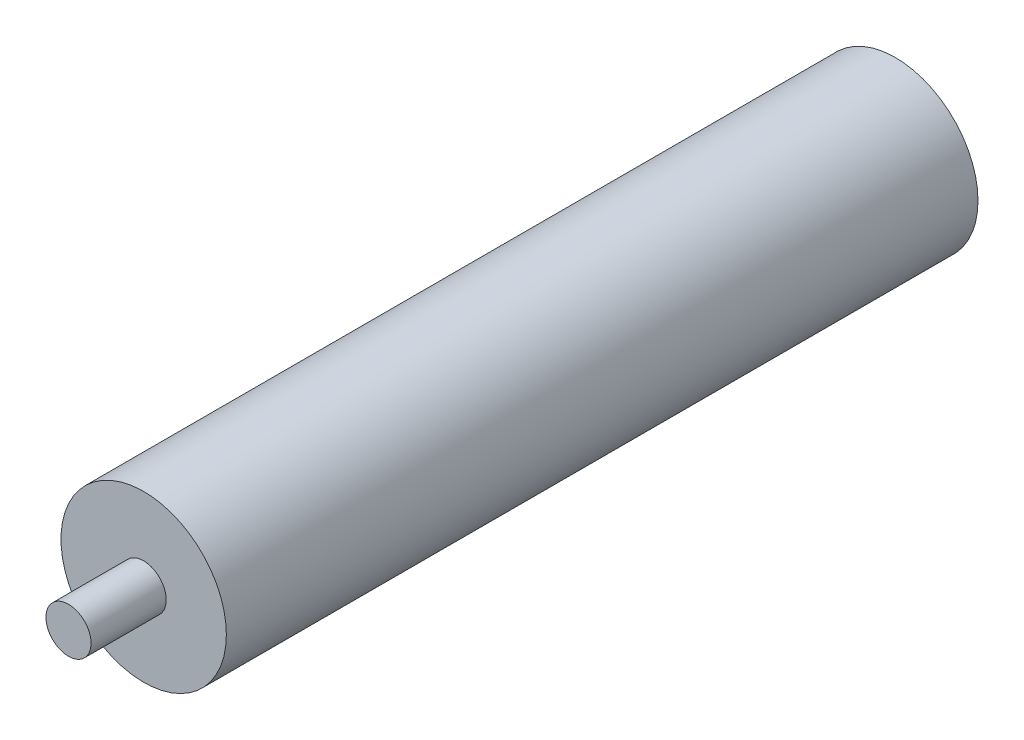
SolidWorks part; units mm, degrees
material "Malleable Cast Iron"
ref_plane "Front Plane" through (0, 0, 0) normal (0, 0, 1) x (1, 0, 0)
ref_plane "Top Plane" through (0, 0, 0) normal (0, 1, 0) x (1, 0, 0)
ref_plane "Right Plane" through (0, 0, 0) normal (1, 0, 0) x (0, 0, -1)
sketch "Sketch1" plane through (0, 0, 0) normal (0, 0, 1) x (1, 0, 0)
  circle A0 centre (0, 0) radius 5.5
extrude "Boss-Extrude1" add sketch "Sketch1" along normal blind 50
sketch "Sketch2" plane through (0, 0, 50) normal (0, 0, 1) x (1, 0, 0)
  circle A0 centre (0, 0) radius 1.5
extrude "Boss-Extrude2" add sketch "Sketch2" along normal blind 5
